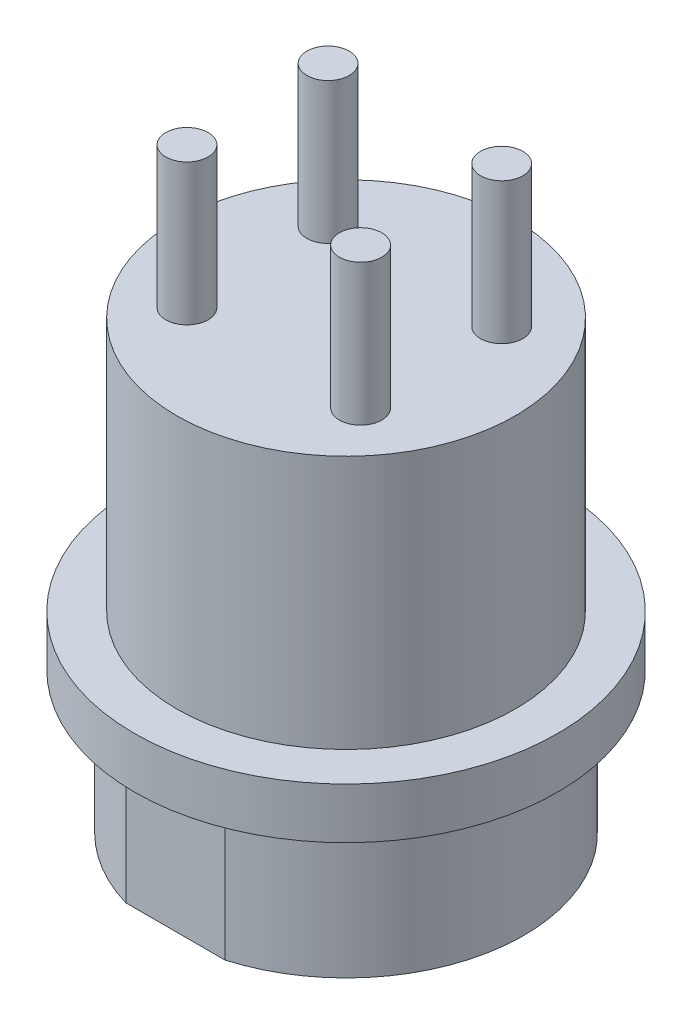
SolidWorks part; units mm, degrees
material "1060 Alloy"
ref_plane "Front Plane" through (0, 0, 0) normal (0, 0, 1) x (1, 0, 0)
ref_plane "Top Plane" through (0, 0, 0) normal (0, 1, 0) x (1, 0, 0)
ref_plane "Right Plane" through (0, 0, 0) normal (1, 0, 0) x (0, 0, -1)
sketch "Sketch1" plane through (0, 0, 0) normal (0, 1, 0) x (1, 0, 0)
  circle A0 centre (0, 0) radius 6.3
  dimension "D1" = 12.6
extrude "Boss-Extrude1" add sketch "Sketch1" along normal blind 5
sketch "Sketch2" plane through (0, 5, 0) normal (0, 1, 0) x (1, 0, 0)
  circle A0 centre (0, 0) radius 7.5
  dimension "D1" = 15
extrude "Boss-Extrude2" add sketch "Sketch2" along normal blind 1.8
sketch "Sketch3" plane through (0, 6.8, 0) normal (0, 1, 0) x (1, 0, 0)
  circle A0 centre (0, 0) radius 6
  dimension "D1" = 12
extrude "Boss-Extrude3" add sketch "Sketch3" along normal blind 9
sketch "Sketch4" plane through (0, 0, 0) normal (0, -1, 0) x (1, 0, 0)
  circle A0 centre (0, 0) radius 4.5
  dimension "D1" = 9
extrude "Cut-Extrude1" cut sketch "Sketch4" against normal blind 10
sketch "Sketch5" plane through (0, 10, 0) normal (0, -1, 0) x (1, 0, 0)
  line L0 (-0.5, 4.5) -> (0.5, 4.5)
  arc A1 (-0.5, 4.5) -> (0.5, 4.5) centre (0, 4.5) ccw
  point P7 (0, 4.5)
  dimension "D1" = 1
extrude "Boss-Extrude4" add sketch "Sketch5" along normal up to surface (10 mm away) up to face at (0, 0, -4.5)
sketch "Sketch6" plane through (0, 10, 0) normal (0, -1, 0) x (1, 0, 0)
  line L0 (-4.5, 0) -> (4.5, 0) construction
  line L1 (0, -4.5) -> (0, 4.5) construction
  line L2 (-2, -2) -> (-2, 2) construction
  line L3 (2, -2) -> (2, 2) construction
  arc A0 (-0.4992, 4.4722) -> (0.4992, 4.4722) centre (0, 0) ccw construction
  arc A1 (-0.4992, 4.4722) -> (0.4992, 4.4722) centre (0, 0) ccw construction
  circle A2 centre (-2, 2) radius 0.5
  circle A3 centre (2, 2) radius 0.5
  circle A4 centre (2, -2) radius 0.5
  circle A5 centre (-2, -2) radius 0.5
  point P15 (-2, 0)
  point P18 (2, 0)
  dimension "D2" = 1
  dimension "D1" = 4
  dimension "D3" = 2
  dimension "D4" = 2
extrude "Boss-Extrude5" add sketch "Sketch6" along normal blind 8
fillet "Fillet1" radius 0.2 4 edges at (-2, 2, -2.5) (2, 2, -2.5) (2, 2, 1.5) (-2, 2, 1.5)
sketch "Sketch7" plane through (0, 15.8, 0) normal (0, 1, 0) x (1, 0, 0)
  line L0 (0, 6) -> (0, -6) construction
  line L1 (-6, 0) -> (6, 0) construction
  line L2 (-3.138, -2.5) -> (-3.138, 2.5) construction
  line L3 (3.0154, -2.5) -> (3.0154, 2.5) construction
  circle A0 centre (0, 0) radius 6 construction
  circle A1 centre (0, 0) radius 6 construction
  circle A2 centre (-3.138, 2.5) radius 0.75
  circle A3 centre (-3.138, -2.5) radius 0.75
  circle A4 centre (3.0154, -2.5) radius 0.75
  circle A5 centre (3.0154, 2.5) radius 0.75
  point P12 (-3.138, 0)
  point P15 (3.0154, 0)
  dimension "D2" = 1.5
  dimension "D1" = 5
extrude "Boss-Extrude6" add sketch "Sketch7" along normal blind 5
sketch "Sketch8" plane through (0, 0, 0) normal (0, -1, 0) x (1, 0, 0)
  line L1 (-5, 6.05) -> (5, 6.05)
  line L2 (-5, 6.05) -> (-5, 6.55)
  line L3 (-5, 6.55) -> (5, 6.55)
  line L4 (5, 6.05) -> (5, 6.55)
  line L5 (-5, 6.05) -> (5, 6.55) construction
  line L6 (-5, 6.55) -> (5, 6.05) construction
  line L7 (-5, -5.7601) -> (5, -5.7601)
  line L8 (-5, -5.7601) -> (-5, -6.8399)
  line L9 (-5, -6.8399) -> (5, -6.8399)
  line L10 (5, -5.7601) -> (5, -6.8399)
  line L11 (-5, -5.7601) -> (5, -6.8399) construction
  line L12 (-5, -6.8399) -> (5, -5.7601) construction
  circle A0 centre (0, 0) radius 6.3 construction
  circle A1 centre (0, 0) radius 6.3 construction
  point P0 (0, 6.3)
  point P9 (0, -6.3)
  dimension "D1" = 10
  dimension "D2" = 0.5
extrude "Cut-Extrude2" cut sketch "Sketch8" against normal up to surface (5 mm away) up to face at (0, 5, 6.3)
